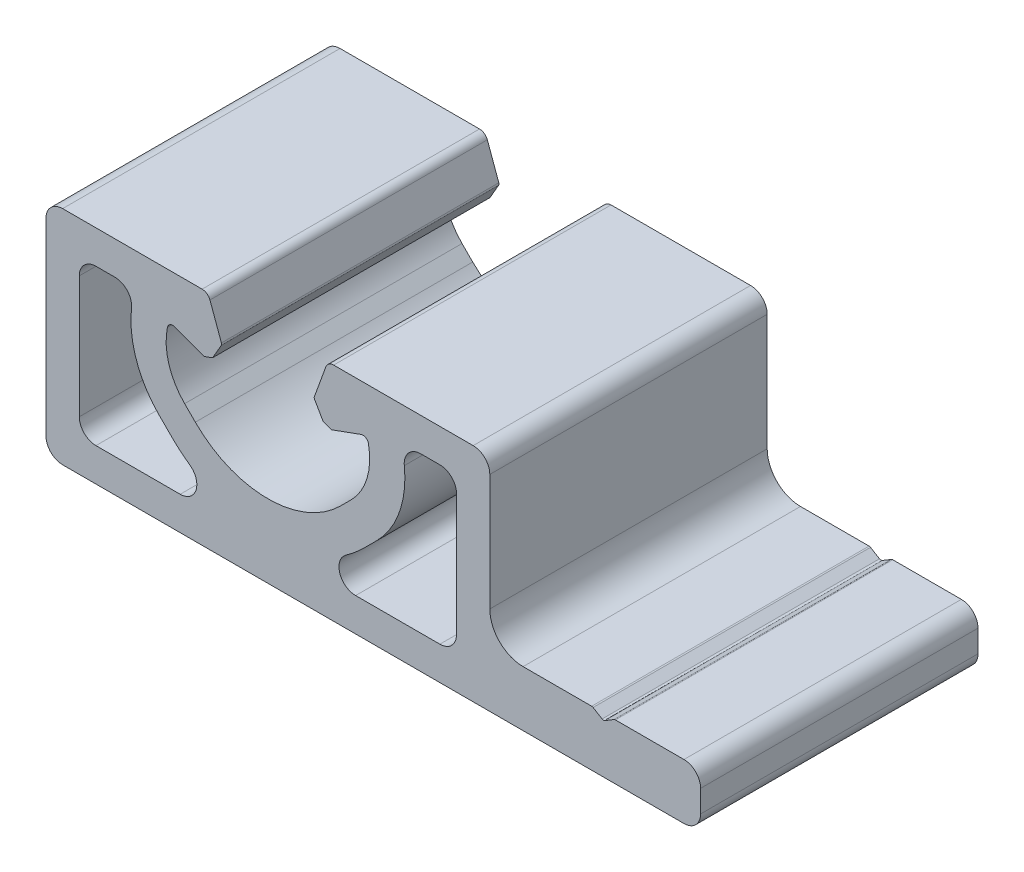
SolidWorks part; units mm, degrees
material "6005-T5"
ref_plane "Front" through (0, 0, 0) normal (0, 0, 1) x (1, 0, 0)
ref_plane "Top" through (0, 0, 0) normal (0, 1, 0) x (1, 0, 0)
ref_plane "Right" through (0, 0, 0) normal (1, 0, 0) x (0, 0, -1)
sketch "Sk Main Extrusion" plane through (0, 0, 0) normal (0, 0, 1) x (1, 0, 0)
  line L32 (-9.7978, 8.2237) -> (-8.6621, 7.0879)
  line L33 (-7.9057, 3) -> (-15.5, 3)
  line L34 (-17, 4.5) -> (-17, 15.5)
  line L35 (-15.5, 17) -> (-13.7838, 17)
  line L36 (17, 15.5) -> (17, 4.5)
  line L37 (15.5, 3) -> (7.9057, 3)
  line L38 (8.6621, 7.0879) -> (9.7978, 8.2237)
  line L39 (13.7838, 17) -> (15.5, 17)
  line L40 (-4.1901, 16.6712) -> (-5.2221, 19.5065)
  line L41 (-5.9268, 20) -> (-18.5, 20)
  line L42 (-20, 18.5) -> (-20, 1.5)
  line L43 (-18.5, 0) -> (37.5, 0)
  line L44 (39, 1.5) -> (39, 3.5)
  line L45 (37.5, 5) -> (31.3193, 5)
  line L46 (31.1906, 4.9643) -> (30.3788, 4.4765)
  line L47 (30.1212, 4.4765) -> (29.3094, 4.9643)
  line L48 (29.1807, 5) -> (23, 5)
  line L49 (20, 8) -> (20, 18.5)
  line L50 (18.5, 20) -> (5.9268, 20)
  line L51 (5.2221, 19.5065) -> (4.1901, 16.6712)
  line L52 (4.2085, 16.4607) -> (4.9876, 15.1113)
  line L53 (4.9876, 15.1113) -> (5.7185, 14.8453)
  line L54 (5.7185, 14.8453) -> (8.3962, 15.8198)
  line L55 (7.5042, 10.2727) -> (6.5407, 9.3093)
  line L56 (-6.5407, 9.3093) -> (-7.5042, 10.2727)
  line L57 (-8.3962, 15.8198) -> (-5.7185, 14.8453)
  line L58 (-5.7185, 14.8453) -> (-4.9876, 15.1113)
  line L59 (-4.9876, 15.1113) -> (-4.2085, 16.4607)
  arc A30 (-12.293, 15.3346) -> (-13.7838, 17) centre (-13.7838, 15.5) ccw
  arc A31 (-12.293, 15.3346) -> (-9.7978, 8.2237) centre (-3.646, 14.3755) ccw
  arc A32 (-8.6621, 7.0879) -> (-7.0433, 5.7273) centre (0, 15.75) ccw
  arc A33 (-7.9057, 3) -> (-7.0433, 5.7273) centre (-7.9057, 4.5) ccw
  arc A34 (-17, 4.5) -> (-15.5, 3) centre (-15.5, 4.5) ccw
  arc A35 (-15.5, 17) -> (-17, 15.5) centre (-15.5, 15.5) ccw
  arc A36 (-5.2221, 19.5065) -> (-5.9268, 20) centre (-5.9268, 19.25) ccw
  arc A37 (-18.5, 20) -> (-20, 18.5) centre (-18.5, 18.5) ccw
  arc A38 (-20, 1.5) -> (-18.5, 0) centre (-18.5, 1.5) ccw
  arc A39 (37.5, 0) -> (39, 1.5) centre (37.5, 1.5) ccw
  arc A40 (39, 3.5) -> (37.5, 5) centre (37.5, 3.5) ccw
  arc A41 (31.3193, 5) -> (31.1906, 4.9643) centre (31.3193, 4.75) ccw
  arc A42 (30.1212, 4.4765) -> (30.3788, 4.4765) centre (30.25, 4.6908) ccw
  arc A43 (29.3094, 4.9643) -> (29.1807, 5) centre (29.1807, 4.75) ccw
  arc A44 (20, 8) -> (23, 5) centre (23, 8) ccw
  arc A45 (20, 18.5) -> (18.5, 20) centre (18.5, 18.5) ccw
  arc A46 (5.9268, 20) -> (5.2221, 19.5065) centre (5.9268, 19.25) ccw
  arc A47 (4.1901, 16.6712) -> (4.2085, 16.4607) centre (4.425, 16.5857) ccw
  arc A48 (9.057, 15.4507) -> (8.3962, 15.8198) centre (8.5672, 15.35) ccw
  arc A49 (7.5042, 10.2727) -> (9.057, 15.4507) centre (3.4737, 14.3032) ccw
  arc A50 (-6.5407, 9.3093) -> (6.5407, 9.3093) centre (0, 15.85) ccw
  arc A51 (-9.057, 15.4507) -> (-7.5042, 10.2727) centre (-3.4737, 14.3032) ccw
  arc A52 (-8.3962, 15.8198) -> (-9.057, 15.4507) centre (-8.5672, 15.35) ccw
  arc A53 (-4.2085, 16.4607) -> (-4.1901, 16.6712) centre (-4.425, 16.5857) ccw
  arc A54 (17, 15.5) -> (15.5, 17) centre (15.5, 15.5) ccw
  arc A55 (15.5, 3) -> (17, 4.5) centre (15.5, 4.5) ccw
  arc A56 (7.0433, 5.7273) -> (7.9057, 3) centre (7.9057, 4.5) ccw
  arc A57 (7.0433, 5.7273) -> (8.6621, 7.0879) centre (0, 15.75) ccw
  arc A58 (9.7978, 8.2237) -> (12.293, 15.3346) centre (3.646, 14.3755) ccw
  arc A59 (13.7838, 17) -> (12.293, 15.3346) centre (13.7838, 15.5) ccw
  point P53 (0, 0)
extrude "Main Extrusion" add sketch "Sk Main Extrusion" against normal blind 25
sketch "Threaded Insert Mate Sketch" plane through (0, 0, 0) normal (0, 0, 1) x (1, 0, 0)
  circle A0 centre (0, 12.7) radius 5.6515
  dimension "D2" = 11.303
  dimension "D1" = 12.7
equation "\"Weight kg\"= round ( \"SW-Mass\" , 2 )"
equation "\"Weight lbs\"= round ( \"SW-Mass\" * 2.2046 , 2 )"
equation "\"Length mm\"= round ( \"Length@Main Extrusion\" , 2 )"
equation "\"Length in\"= round ( \"Length@Main Extrusion\" / 25.4 , 3 )"
